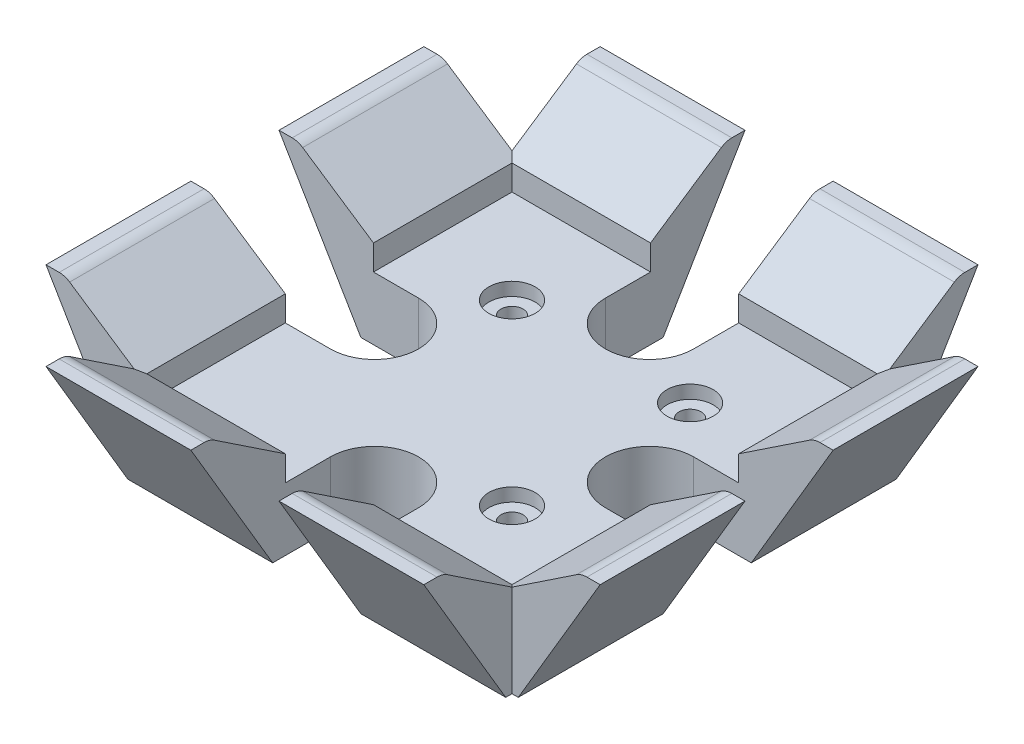
SolidWorks part; units mm, degrees
ref_plane "Front Plane" through (0, 0, 0) normal (0, 0, 1) x (1, 0, 0)
ref_plane "Top Plane" through (0, 0, 0) normal (0, 1, 0) x (1, 0, 0)
ref_plane "Right Plane" through (0, 0, 0) normal (1, 0, 0) x (0, 0, -1)
sketch "Sketch1" plane through (0, 0, 0) normal (0, 1, 0) x (1, 0, 0)
  line L1 (-29, -29) -> (29, -29)
  line L2 (-29, -29) -> (-29, 29)
  line L3 (-29, 29) -> (29, 29)
  line L4 (29, -29) -> (29, 29)
  line L5 (-29, -29) -> (29, 29) construction
  line L6 (-29, 29) -> (29, -29) construction
  point P0 (0, 0)
  dimension "D1" = 58
  dimension "D2" = 58
extrude "Boss-Extrude1" add sketch "Sketch1" along normal blind 10
sketch "Sketch2" plane through (0, 0, 0) normal (0, 0, 1) x (1, 0, 0)
  line L0 (29, 0) -> (29, 14)
  line L1 (29, 10) -> (29, 0) construction
  line L2 (-29, 0) -> (29, 0) construction
  line L3 (-29, 10) -> (29, 10) construction
  line L4 (29, 0) -> (31, 0)
  line L5 (31, 0) -> (44, 22)
  line L6 (29, 14) -> (40.2442, 21.4962)
  line L7 (41.9083, 22) -> (44, 22)
  arc A0 (40.2442, 21.4962) -> (41.9083, 22) centre (41.9083, 19) cw
  point P16 (41, 22)
  dimension "D3" = 3
  dimension "D4" = 13
  dimension "D7" = 3
  dimension "D1" = 4
  dimension "D5" = 12
  dimension "D6" = 2
extrude "Boss-Extrude3" add sketch "Sketch2" along normal mid plane 60.01
sketch "Sketch6" plane through (0, 0, 0) normal (0, 0, 1) x (1, 0, 0)
  line L0 (0, -13.4563) -> (0, 32.8266) construction
pattern_circular "CirPattern7" count 4 over 360 about axis through (0, 0, 0) along (0, 1, 0) of "Boss-Extrude3"
sketch "Sketch7" plane through (0, 10, 0) normal (0, 1, 0) x (1, 0, 0)
  line L0 (21.84, 7) -> (54.5273, 7)
  line L1 (54.5273, 7) -> (54.5273, -7)
  line L2 (54.5273, -7) -> (21.84, -7)
  line L3 (7, -21.84) -> (7, -54.5273)
  line L4 (-7, -54.5273) -> (-7, -21.84)
  line L5 (7, -54.5273) -> (-7, -54.5273)
  line L6 (-21.84, -7) -> (-54.5273, -7)
  line L7 (-54.5273, 7) -> (-21.84, 7)
  line L8 (-54.5273, -7) -> (-54.5273, 7)
  line L9 (-7, 21.84) -> (-7, 54.5273)
  line L10 (7, 54.5273) -> (7, 21.84)
  line L11 (-7, 54.5273) -> (7, 54.5273)
  arc A0 (21.84, 7) -> (21.84, -7) centre (21.84, 0) ccw construction
  arc A1 (21.84, 7) -> (21.84, -7) centre (21.84, 0) ccw
  arc A2 (7, -21.84) -> (-7, -21.84) centre (0, -21.84) ccw
  arc A3 (-21.84, -7) -> (-21.84, 7) centre (-21.84, 0) ccw
  arc A4 (-7, 21.84) -> (7, 21.84) centre (0, 21.84) ccw
  point P23 (0, 0)
  dimension "D1" = 4
extrude "Cut-Extrude1" cut sketch "Sketch7" against normal through all both and the other way through all
extrude "Cut-Extrude2" cut sketch "Sketch8" against normal blind 20
sketch "Sketch8" plane through (-225.294, 10, 60.7775) normal (0, 1, 0) x (0, 0, -1)
  line L0 (60.7775, -225.294) -> (84.0315, -202.04) construction
  line L1 (60.7775, -225.294) -> (117.7906, -225.294) construction
  circle A0 centre (74.9197, -211.1519) radius 1.75
  circle A1 centre (74.9197, -239.4362) radius 1.75
  circle A2 centre (46.6354, -239.4362) radius 1.75
  point P15 (60.7775, -225.294)
sketch "Sketch9" plane through (0, 10, 0) normal (0, 1, 0) x (1, 0, 0)
  circle A0 centre (-14.1421, 14.1421) radius 3.665
  circle A1 centre (14.1421, -14.1421) radius 3.665
  circle A2 centre (14.1421, 14.1421) radius 3.665
  dimension "D1" = 7.33
extrude "Cut-Extrude3" cut sketch "Sketch9" against normal blind 2.1
